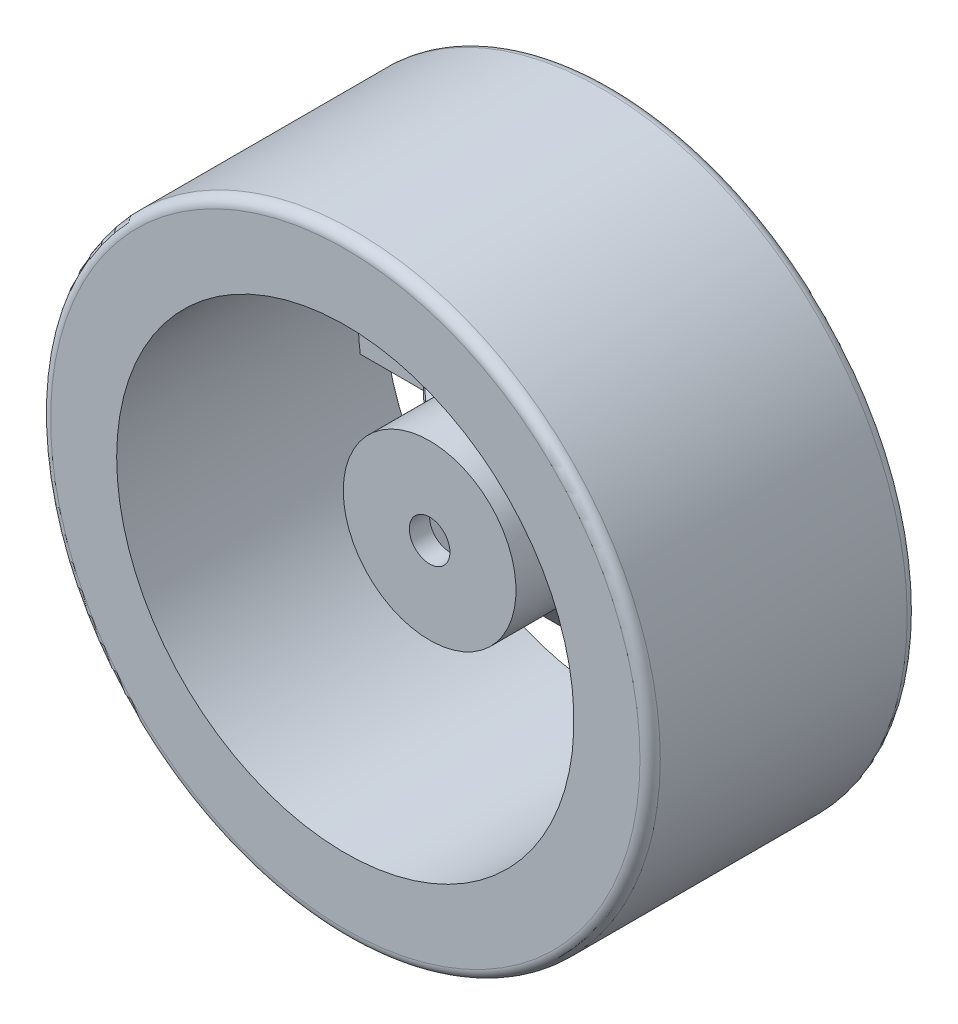
SolidWorks part; units mm, degrees
ref_plane "前视基准面" through (0, 0, 0) normal (0, 0, 1) x (1, 0, 0)
ref_plane "上视基准面" through (0, 0, 0) normal (0, 1, 0) x (1, 0, 0)
ref_plane "右视基准面" through (0, 0, 0) normal (1, 0, 0) x (0, 0, -1)
sketch "草图1" plane through (0, 0, 0) normal (0, 0, 1) x (1, 0, 0)
  circle A0 centre (0, 0) radius 30
  dimension "D1" = 60
extrude "凸台-拉伸1" add sketch "草图1" along normal blind 26.3
sketch "草图2" plane through (0, 0, 0) normal (0, 0, -1) x (-1, 0, 0)
  circle A0 centre (0, 0) radius 22.5
  dimension "D1" = 45
extrude "切除-拉伸1" cut sketch "草图2" against normal through all
ref_plane "基准面1" through (0, 0, 10) normal (0, 0, -1) x (-1, 0, 0)
sketch "草图3" plane through (0, 0, 10) normal (0, 0, -1) x (-1, 0, 0)
  circle A0 centre (0, 0) radius 8.5
  circle A1 centre (0, 0) radius 2
  point P5 (-0.3962, 0)
  dimension "D1" = 17
  dimension "D2" = 4
extrude "凸台-拉伸2" add sketch "草图3" against normal blind 8 separate body contours A0
sketch "草图4" plane through (0, 0, 10) normal (0, 0, -1) x (-1, 0, 0)
  line L1 (7.2169, 0) -> (3.6084, 6.25)
  line L2 (3.6084, 6.25) -> (-3.6084, 6.25)
  line L3 (-3.6084, 6.25) -> (-7.2169, 0)
  line L4 (-7.2169, 0) -> (-3.6084, -6.25)
  line L5 (-3.6084, -6.25) -> (3.6084, -6.25)
  line L6 (3.6084, -6.25) -> (7.2169, 0)
  circle A0 centre (0, 0) radius 7.2169 construction
  dimension "D1" = 12.5
extrude "切除-拉伸2" cut sketch "草图4" against normal offset from surface (6 mm away) 2 up to face at (-2, 0, 18)
sketch "草图5" plane through (0, 0, 0) normal (0, 1, 0) x (1, 0, 0)
  line L0 (-22.5, 0) -> (-15.2751, 0)
  line L1 (22.5, 0) -> (-22.5, 0) construction
  line L2 (-15.2751, 0) -> (-7.2431, -10)
  line L3 (33, -10) -> (-33, -10) construction
  line L4 (-22.5, 0) -> (-24.165, 0)
  line L5 (30, 0) -> (-30, 0) construction
  line L6 (-24.165, 0) -> (-24.165, -2.5291)
  line L7 (-24.165, -2.5291) -> (-16.0699, -2.5291)
  line L8 (-16.0699, -2.5291) -> (-8.3968, -10)
  line L9 (-8.3968, -10) -> (-7.2431, -10)
  point P13 (-16.0699, -2.5291)
  point P15 (-15.2751, 0)
extrude "凸台-拉伸3" add sketch "草图5" along normal mid plane 6
pattern_circular "阵列(圆周)1" count 7 over 360 about axis through (0, 0, 0) along (0, 0, 1) of "凸台-拉伸3"
fillet "圆角1" radius 1 2 edges at (30, 0, 0) (30, 0, 26.3)
